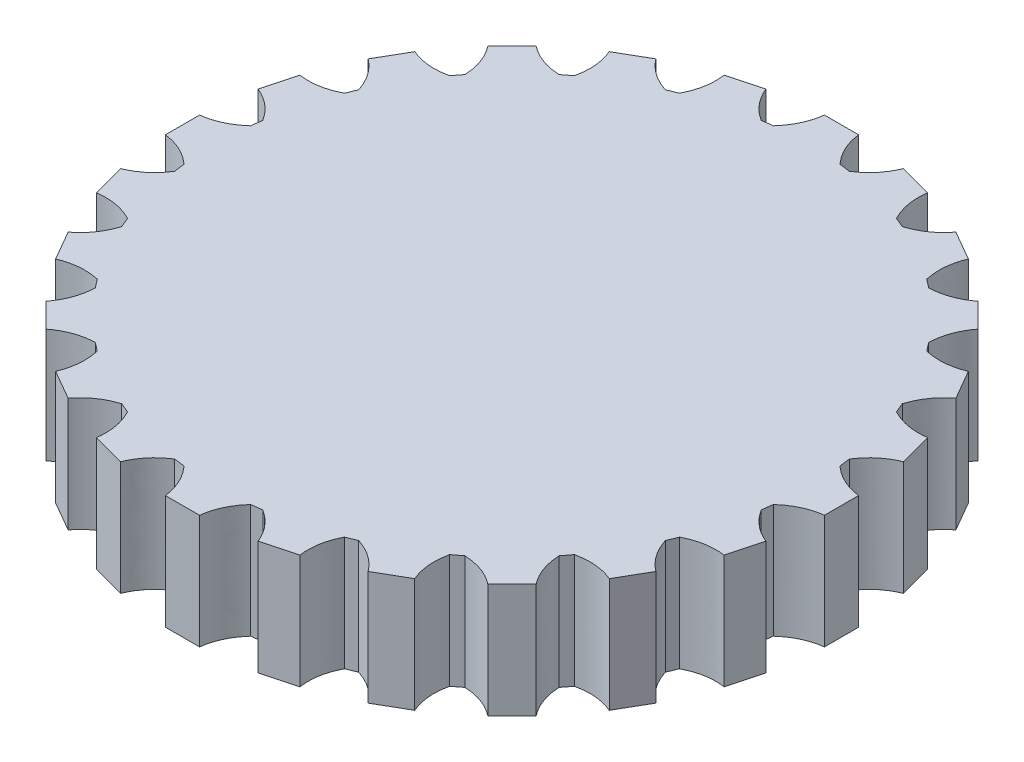
SolidWorks part; units mm, degrees
ref_plane "Front Plane" through (0, 0, 0) normal (0, 0, 1) x (1, 0, 0)
ref_plane "Top Plane" through (0, 0, 0) normal (0, 1, 0) x (1, 0, 0)
ref_plane "Right Plane" through (0, 0, 0) normal (1, 0, 0) x (0, 0, -1)
sketch "Sketch2" plane through (0, 0, 0) normal (0, 1, 0) x (1, 0, 0)
  line L0 (0, 7.0154) -> (0, -8.5846) construction
  line L1 (-0.2247, 4.334) -> (0.2247, 4.334)
  line L2 (0.9047, 4.2445) -> (1.3388, 4.1282)
  line L3 (1.9725, 3.8657) -> (2.3616, 3.6411)
  line L4 (2.9058, 3.2235) -> (3.2235, 2.9058)
  line L5 (3.6411, 2.3616) -> (3.8657, 1.9725)
  line L6 (4.1282, 1.3388) -> (4.2445, 0.9047)
  line L7 (4.334, 0.2247) -> (4.334, -0.2247)
  line L8 (4.2445, -0.9047) -> (4.1282, -1.3388)
  line L9 (3.8657, -1.9725) -> (3.6411, -2.3616)
  line L10 (3.2235, -2.9058) -> (2.9058, -3.2235)
  line L11 (2.3616, -3.6411) -> (1.9725, -3.8657)
  line L12 (1.3388, -4.1282) -> (0.9047, -4.2445)
  line L13 (0.2247, -4.334) -> (-0.2247, -4.334)
  line L14 (-0.9047, -4.2445) -> (-1.3388, -4.1282)
  line L15 (-1.9725, -3.8657) -> (-2.3616, -3.6411)
  line L16 (-2.9058, -3.2235) -> (-3.2235, -2.9058)
  line L17 (-3.6411, -2.3616) -> (-3.8657, -1.9725)
  line L18 (-4.1282, -1.3388) -> (-4.2445, -0.9047)
  line L19 (-4.334, -0.2247) -> (-4.334, 0.2247)
  line L20 (-4.2445, 0.9047) -> (-4.1282, 1.3388)
  line L21 (-3.8657, 1.9725) -> (-3.6411, 2.3616)
  line L22 (-3.2235, 2.9058) -> (-2.9058, 3.2235)
  line L23 (-2.3616, 3.6411) -> (-1.9725, 3.8657)
  line L24 (-1.3388, 4.1282) -> (-0.9047, 4.2445)
  circle A1 centre (0, 0) radius 3.9
  spline S0 degree 2 poles (-0.438, 3.8753) (-0.257, 4.0738) (-0.2247, 4.334) knots 0 0 0 1 1 1
  spline S1 degree 2 poles (0.438, 3.8753) (0.257, 4.0738) (0.2247, 4.334) knots 0 0 0 1 1 1
  spline S2 degree 2 poles (0.58, 3.8566) (0.8062, 4.0015) (0.9047, 4.2445) knots 0 0 0 1 1 1
  spline S3 degree 2 poles (1.426, 3.6299) (1.3026, 3.8685) (1.3388, 4.1282) knots 0 0 0 1 1 1
  spline S4 degree 2 poles (1.5584, 3.5751) (1.8144, 3.6565) (1.9725, 3.8657) knots 0 0 0 1 1 1
  spline S5 degree 2 poles (2.317, 3.1372) (2.2595, 3.3996) (2.3616, 3.6411) knots 0 0 0 1 1 1
  spline S6 degree 2 poles (2.4306, 3.05) (2.6989, 3.0624) (2.9058, 3.2235) knots 0 0 0 1 1 1
  spline S7 degree 2 poles (3.05, 2.4306) (3.0624, 2.6989) (3.2235, 2.9058) knots 0 0 0 1 1 1
  spline S8 degree 2 poles (3.1372, 2.317) (3.3996, 2.2595) (3.6411, 2.3616) knots 0 0 0 1 1 1
  spline S9 degree 2 poles (3.5751, 1.5584) (3.6565, 1.8144) (3.8657, 1.9725) knots 0 0 0 1 1 1
  spline S10 degree 2 poles (3.6299, 1.426) (3.8685, 1.3026) (4.1282, 1.3388) knots 0 0 0 1 1 1
  spline S11 degree 2 poles (3.8566, 0.58) (4.0015, 0.8062) (4.2445, 0.9047) knots 0 0 0 1 1 1
  spline S12 degree 2 poles (3.8753, 0.438) (4.0738, 0.257) (4.334, 0.2247) knots 0 0 0 1 1 1
  spline S13 degree 2 poles (3.8753, -0.438) (4.0738, -0.257) (4.334, -0.2247) knots 0 0 0 1 1 1
  spline S14 degree 2 poles (3.8566, -0.58) (4.0015, -0.8062) (4.2445, -0.9047) knots 0 0 0 1 1 1
  spline S15 degree 2 poles (3.6299, -1.426) (3.8685, -1.3026) (4.1282, -1.3388) knots 0 0 0 1 1 1
  spline S16 degree 2 poles (3.5751, -1.5584) (3.6565, -1.8144) (3.8657, -1.9725) knots 0 0 0 1 1 1
  spline S17 degree 2 poles (3.1372, -2.317) (3.3996, -2.2595) (3.6411, -2.3616) knots 0 0 0 1 1 1
  spline S18 degree 2 poles (3.05, -2.4306) (3.0624, -2.6989) (3.2235, -2.9058) knots 0 0 0 1 1 1
  spline S19 degree 2 poles (2.4306, -3.05) (2.6989, -3.0624) (2.9058, -3.2235) knots 0 0 0 1 1 1
  spline S20 degree 2 poles (2.317, -3.1372) (2.2595, -3.3996) (2.3616, -3.6411) knots 0 0 0 1 1 1
  spline S21 degree 2 poles (1.5584, -3.5751) (1.8144, -3.6565) (1.9725, -3.8657) knots 0 0 0 1 1 1
  spline S22 degree 2 poles (1.426, -3.6299) (1.3026, -3.8685) (1.3388, -4.1282) knots 0 0 0 1 1 1
  spline S23 degree 2 poles (0.58, -3.8566) (0.8062, -4.0015) (0.9047, -4.2445) knots 0 0 0 1 1 1
  spline S24 degree 2 poles (0.438, -3.8753) (0.257, -4.0738) (0.2247, -4.334) knots 0 0 0 1 1 1
  spline S25 degree 2 poles (-0.438, -3.8753) (-0.257, -4.0738) (-0.2247, -4.334) knots 0 0 0 1 1 1
  spline S26 degree 2 poles (-0.58, -3.8566) (-0.8062, -4.0015) (-0.9047, -4.2445) knots 0 0 0 1 1 1
  spline S27 degree 2 poles (-1.426, -3.6299) (-1.3026, -3.8685) (-1.3388, -4.1282) knots 0 0 0 1 1 1
  spline S28 degree 2 poles (-1.5584, -3.5751) (-1.8144, -3.6565) (-1.9725, -3.8657) knots 0 0 0 1 1 1
  spline S29 degree 2 poles (-2.317, -3.1372) (-2.2595, -3.3996) (-2.3616, -3.6411) knots 0 0 0 1 1 1
  spline S30 degree 2 poles (-2.4306, -3.05) (-2.6989, -3.0624) (-2.9058, -3.2235) knots 0 0 0 1 1 1
  spline S31 degree 2 poles (-3.05, -2.4306) (-3.0624, -2.6989) (-3.2235, -2.9058) knots 0 0 0 1 1 1
  spline S32 degree 2 poles (-3.1372, -2.317) (-3.3996, -2.2595) (-3.6411, -2.3616) knots 0 0 0 1 1 1
  spline S33 degree 2 poles (-3.5751, -1.5584) (-3.6565, -1.8144) (-3.8657, -1.9725) knots 0 0 0 1 1 1
  spline S34 degree 2 poles (-3.6299, -1.426) (-3.8685, -1.3026) (-4.1282, -1.3388) knots 0 0 0 1 1 1
  spline S35 degree 2 poles (-3.8566, -0.58) (-4.0015, -0.8062) (-4.2445, -0.9047) knots 0 0 0 1 1 1
  spline S36 degree 2 poles (-3.8753, -0.438) (-4.0738, -0.257) (-4.334, -0.2247) knots 0 0 0 1 1 1
  spline S37 degree 2 poles (-3.8753, 0.438) (-4.0738, 0.257) (-4.334, 0.2247) knots 0 0 0 1 1 1
  spline S38 degree 2 poles (-3.8566, 0.58) (-4.0015, 0.8062) (-4.2445, 0.9047) knots 0 0 0 1 1 1
  spline S39 degree 2 poles (-3.6299, 1.426) (-3.8685, 1.3026) (-4.1282, 1.3388) knots 0 0 0 1 1 1
  spline S40 degree 2 poles (-3.5751, 1.5584) (-3.6565, 1.8144) (-3.8657, 1.9725) knots 0 0 0 1 1 1
  spline S41 degree 2 poles (-3.1372, 2.317) (-3.3996, 2.2595) (-3.6411, 2.3616) knots 0 0 0 1 1 1
  spline S42 degree 2 poles (-3.05, 2.4306) (-3.0624, 2.6989) (-3.2235, 2.9058) knots 0 0 0 1 1 1
  spline S43 degree 2 poles (-2.4306, 3.05) (-2.6989, 3.0624) (-2.9058, 3.2235) knots 0 0 0 1 1 1
  spline S44 degree 2 poles (-2.317, 3.1372) (-2.2595, 3.3996) (-2.3616, 3.6411) knots 0 0 0 1 1 1
  spline S45 degree 2 poles (-1.5584, 3.5751) (-1.8144, 3.6565) (-1.9725, 3.8657) knots 0 0 0 1 1 1
  spline S46 degree 2 poles (-1.426, 3.6299) (-1.3026, 3.8685) (-1.3388, 4.1282) knots 0 0 0 1 1 1
  spline S47 degree 2 poles (-0.58, 3.8566) (-0.8062, 4.0015) (-0.9047, 4.2445) knots 0 0 0 1 1 1
  point P12 (0, 4.334)
  dimension "D1" = 7.8
  dimension "D2" = 28
extrude "Boss-Extrude2" add sketch "Sketch2" against normal blind 1.5 contours L0 A1 | A1 L0 | L0 L1 S0 A1 | L1 L0 A1 S1 | A1 S3 L2 S2 | A1 S5 L3 S4 | A1 S7 L4 S6 | A1 S9 L5 S8 | A1 S11 L6 S10 | A1 S13 L7 S12 | A1 S15 L8 S14 | A1 S17 L9 S16 | A1 S19 L10 S18 | A1 S21 L11 S20 | A1 S23 L12 S22 | A1 L0 L13 S24 | L0 A1 S25 L13 | A1 S27 L14 S26 | A1 S29 L15 S28 | A1 S31 L16 S30 | A1 S33 L17 S32 | A1 S35 L18 S34 | A1 S37 L19 S36 | A1 S39 L20 S38 | A1 S41 L21 S40 | A1 S43 L22 S42 | A1 S45 L23 S44 | A1 S47 L24 S46
sketch "Sketch3" plane through (0, -1.5, 0) normal (0, -1, 0) x (1, 0, 0)
  circle A2 centre (0, 0) radius 3.8
extrude "Cut-Extrude1" cut sketch "Sketch3" against normal blind 1.3
